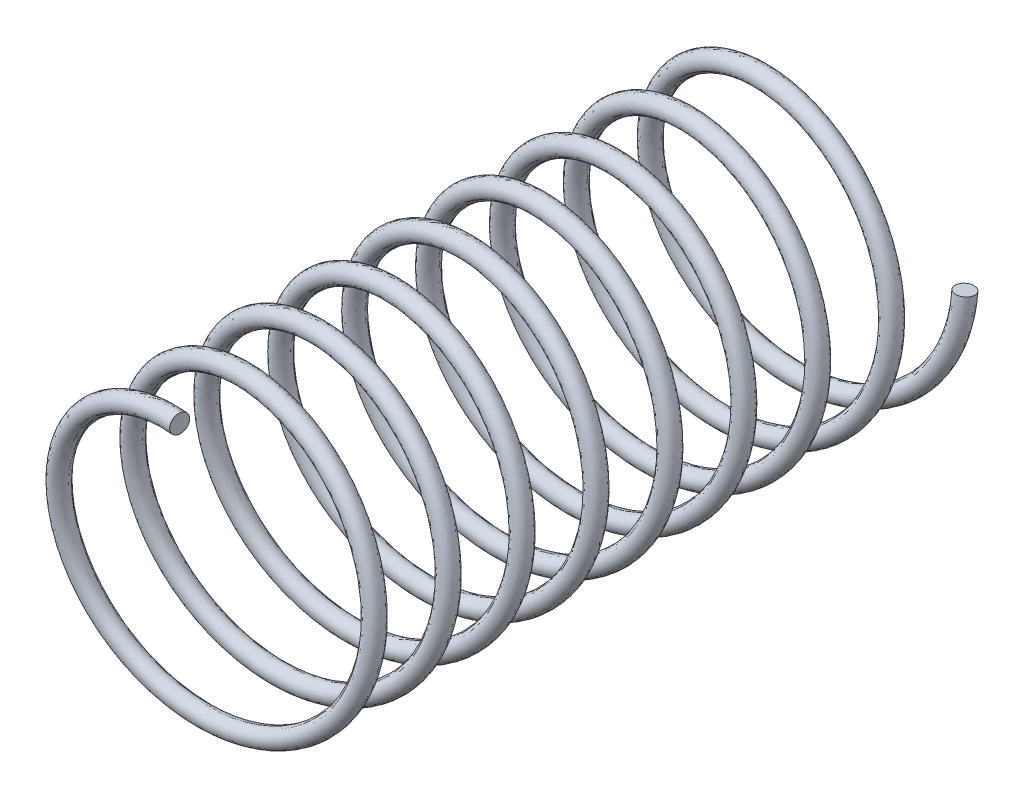
SolidWorks part; units mm, degrees
ref_plane "Front Plane" through (0, 0, 0) normal (0, 0, 1) x (1, 0, 0)
ref_plane "Top Plane" through (0, 0, 0) normal (0, 1, 0) x (1, 0, 0)
ref_plane "Right Plane" through (0, 0, 0) normal (1, 0, 0) x (0, 0, -1)
sketch "Sketch1" plane through (0, 0, 0) normal (0, 0, 1) x (1, 0, 0)
  circle A0 centre (0, 0) radius 150
  dimension "D1" = 300
curve "Helix/Spiral2" pitch 80 height 700 turns 8.75
sweep "Sweep1" add path "Helix/Spiral2" circular profile diameter 20 parameters "D3"=20
